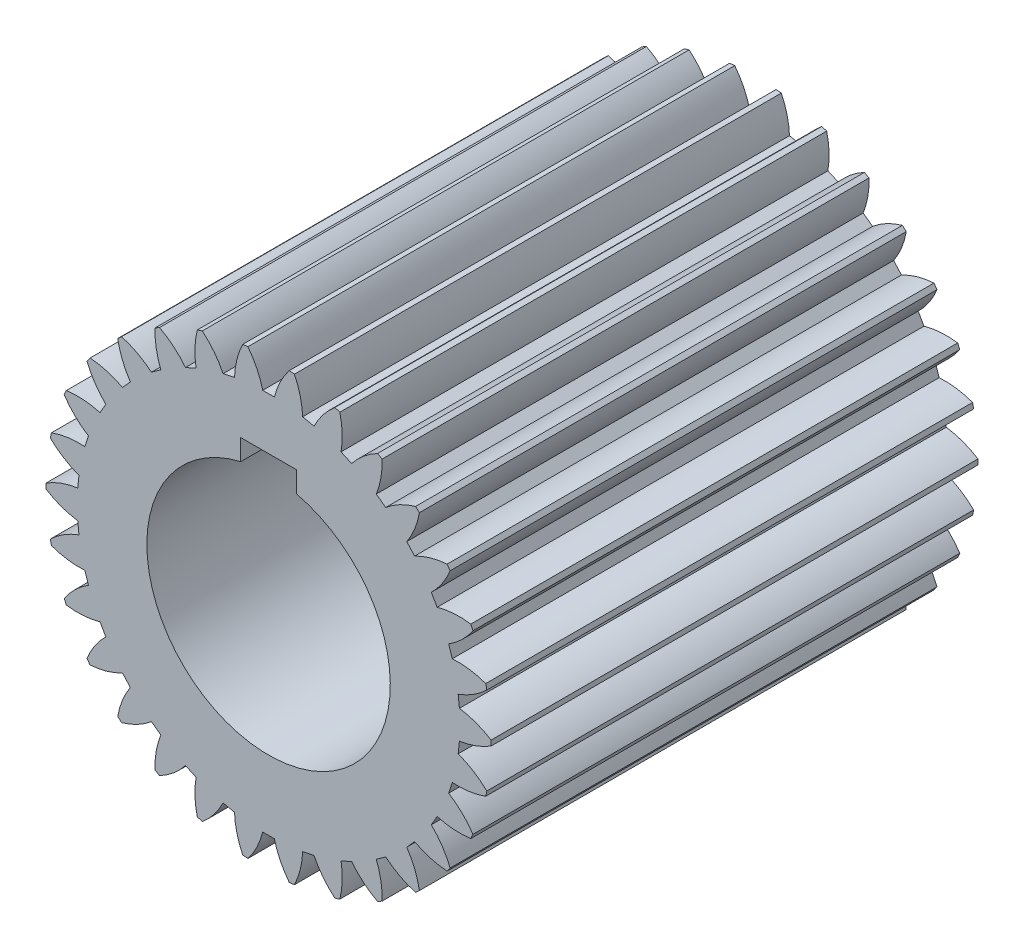
SolidWorks part; units mm, degrees
ref_plane "Front Plane" through (0, 0, 0) normal (0, 0, 1) x (1, 0, 0)
ref_plane "Top Plane" through (0, 0, 0) normal (0, 1, 0) x (1, 0, 0)
ref_plane "Right Plane" through (0, 0, 0) normal (1, 0, 0) x (0, 0, -1)
sketch "Sketch1" plane through (0, 0, 0) normal (0, 0, 1) x (1, 0, 0)
  circle A0 centre (0, 0) radius 30
  circle A1 centre (0, 0) radius 27.5
  circle A2 centre (0, 0) radius 32
  dimension "D1" = 64
  dimension "D2" = 60
  dimension "D3" = 55
extrude "Boss-Extrude1" add sketch "Sketch1" along normal blind 70 contours A2
sketch "Sketch3" plane through (0, 0, 70) normal (0, 0, 1) x (1, 0, 0)
  line L0 (0, 0) -> (0, -14.5028) construction
  line L1 (0, 0) -> (-2.0785, 39.6605) construction
  line L3 (3.0822, 32) -> (-3.0822, 32)
  line L4 (0.839, 27.5) -> (-0.839, 27.5)
  arc A0 (-0.839, 27.5) -> (-3.0822, 32) centre (-12.199, 24.6462) ccw
  circle A1 centre (0, 0) radius 32 construction
  arc A2 (0.839, 27.5) -> (3.0822, 32) centre (12.199, 24.6462) cw
  circle A5 centre (0, 0) radius 27.5 construction
  point P8 (0, 32)
  point P12 (0, 27.5)
  dimension "D1" = 3
extrude "Cut-Extrude1" cut sketch "Sketch3" against normal blind 70
pattern_circular "CirPattern1" count 30 over 360 about axis through (0, 0, 0) along (0, 0, 1) of "Cut-Extrude1"
sketch "Sketch4" plane through (0, 0, 70) normal (0, 0, 1) x (1, 0, 0)
  line L6 (-4, 17.0367) -> (-4, 20.0367)
  line L7 (-4, 20.0367) -> (4, 20.0367)
  line L8 (4, 17.0367) -> (4, 20.0367)
  arc A0 (-4, 17.0367) -> (4, 17.0367) centre (0, 0) ccw
  dimension "D1" = 35
  dimension "D2" = 3
  dimension "D3" = 8
  dimension "D4" = 4
extrude "Cut-Extrude2" cut sketch "Sketch4" against normal blind 70
equation "\"module\"= 2"
equation "\"teeth\"= 30"
equation "\"D1@Sketch1\"=\"module\"*(\"teeth\"+2)"
equation "\"D2@Sketch1\"=\"module\"*\"teeth\""
equation "\"D3@Sketch1\"=\"module\"*(\"teeth\"-2.5)"
equation "\"D1@Sketch3\"=360/(\"teeth\"*4)"
equation "\"D1@CirPattern1\"=\"teeth\""
